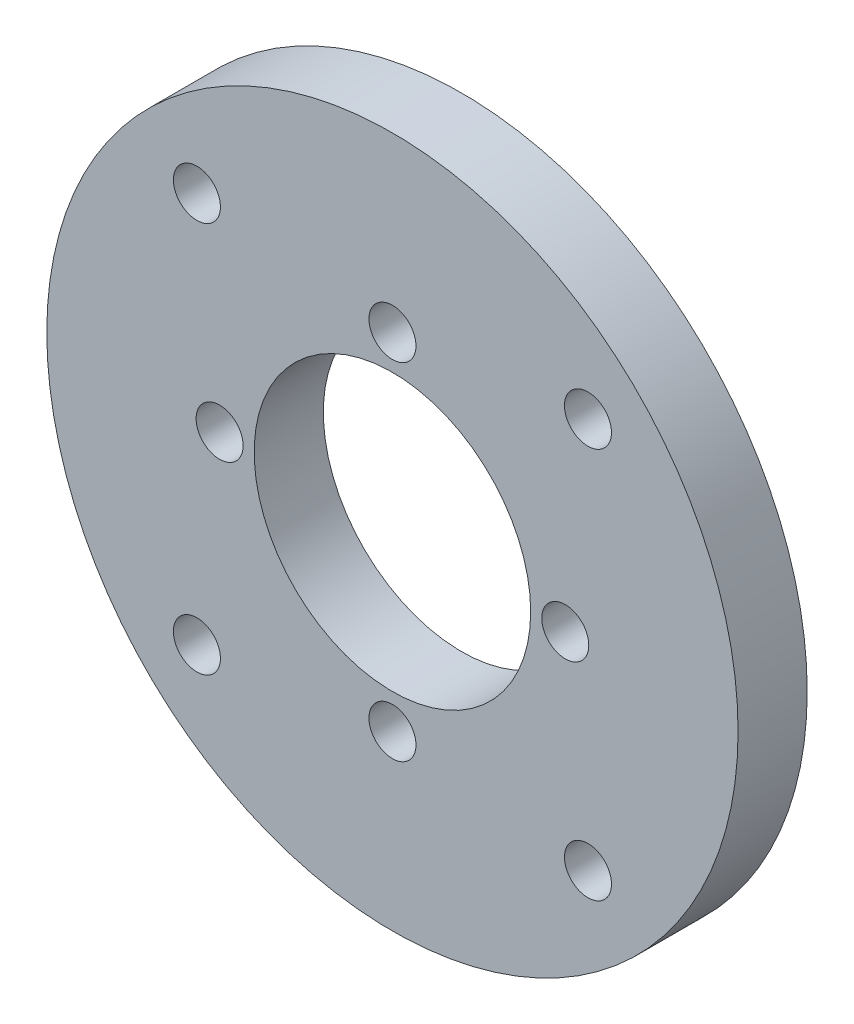
SolidWorks part; units mm, degrees
material "1060 Alloy"
ref_plane "Front Plane" through (0, 0, 0) normal (0, 0, 1) x (1, 0, 0)
ref_plane "Top Plane" through (0, 0, 0) normal (0, 1, 0) x (1, 0, 0)
ref_plane "Right Plane" through (0, 0, 0) normal (1, 0, 0) x (0, 0, -1)
sketch "Sketch1" plane through (0, 0, 0) normal (0, 0, 1) x (1, 0, 0)
  circle A0 centre (0, 0) radius 10
  circle A1 centre (0, 0) radius 25
  dimension "D1" = 20
  dimension "D2" = 50
extrude "Boss-Extrude1" add sketch "Sketch1" along normal blind 5
hole_wizard "M3 Clearance Hole1" positions "Sketch2" profile "Sketch4" hole size "M3" standard "ISO"
sketch "Sketch2" plane through (0, 0, 5) normal (0, 0, 1) x (1, 0, 0)
  point P0 (0, 12.5)
  dimension "D1" = 12.5
sketch "Sketch4" plane through (0, 12.5, 5) normal (1, 0, 0) x (0, -1, 0)
  line L0 (0, 0) -> (0, 8.5215)
  line L1 (0, 8.5215) -> (1.7, 7.5)
  line L2 (1.7, 7.5) -> (1.7, 0)
  line L5 (1.7, 0) -> (0, 0)
  line L10 (0, 8.5215) -> (-1.7, 7.5) construction
  line L11 (0, -6.35) -> (0, 107.95) construction
  dimension "Hole Dia." = 3.4
  dimension "Hole Depth" = 7.5
  dimension "Drill Angle" = 118
pattern_circular "CirPattern1" count 4 over 360 about axis through (0, 0, 0) along (0, 0, 1) of "M3 Clearance Hole1"
hole_wizard "M3 Clearance Hole2" positions "Sketch5" profile "Sketch6" hole size "M3" standard "ISO"
sketch "Sketch5" plane through (0, 0, 5) normal (0, 0, 1) x (1, 0, 0)
  line L0 (0, 0) -> (31.3667, 0) construction
  line L3 (0, 0) -> (14.1421, 14.1421) construction
  point P0 (14.1421, 14.1421)
  dimension "D1" = 20
  dimension "D2" = 45
sketch "Sketch6" plane through (14.1421, 14.1421, 5) normal (1, 0, 0) x (0, -1, 0)
  line L0 (0, 0) -> (0, 8.5215)
  line L1 (0, 8.5215) -> (1.7, 7.5)
  line L2 (1.7, 7.5) -> (1.7, 0)
  line L5 (1.7, 0) -> (0, 0)
  line L10 (0, 8.5215) -> (-1.7, 7.5) construction
  line L11 (0, -6.35) -> (0, 107.95) construction
  dimension "Hole Dia." = 3.4
  dimension "Hole Depth" = 7.5
  dimension "Drill Angle" = 118
pattern_circular "CirPattern2" count 4 over 360 about axis through (0, 0, 0) along (0, 0, 1) of "M3 Clearance Hole2"
